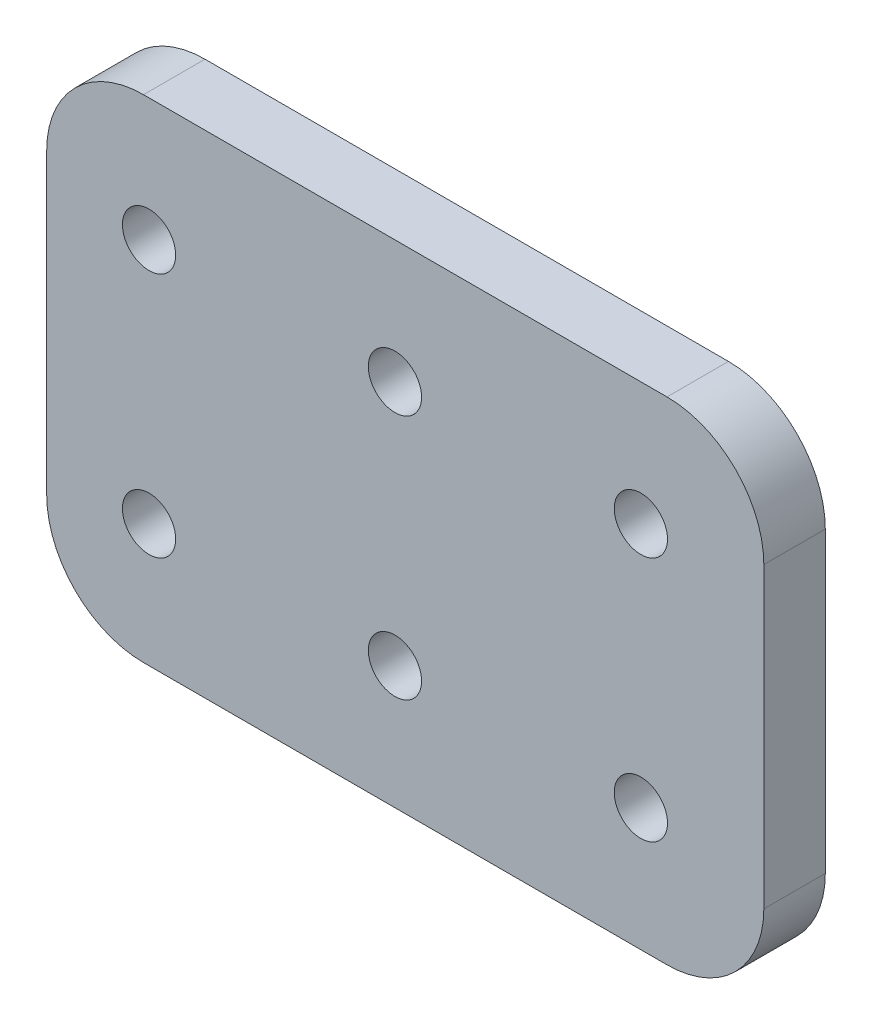
SolidWorks part; units mm, degrees
material "6061-T6 (SS)"
ref_plane "Front" through (0, 0, 0) normal (0, 0, 1) x (1, 0, 0)
ref_plane "Top" through (0, 0, 0) normal (0, 1, 0) x (1, 0, 0)
ref_plane "Right" through (0, 0, 0) normal (1, 0, 0) x (0, 0, -1)
sketch "Sketch1" plane through (0, 0, 0) normal (0, 0, 1) x (1, 0, 0)
  line L0 (-37.035, 25.4) -> (-39.165, 25.4) construction
  line L1 (37.035, -25.4) -> (-37.035, -25.4)
  line L2 (37.035, -25.4) -> (37.035, 25.4)
  line L3 (37.035, 25.4) -> (-37.035, 25.4)
  line L4 (-37.035, -25.4) -> (-37.035, 25.4)
  line L5 (37.035, -25.4) -> (-37.035, 25.4) construction
  line L6 (37.035, 25.4) -> (-37.035, -25.4) construction
  line L7 (-39.165, 25.4) -> (-39.165, -25.4) construction
  line L8 (-39.165, -25.4) -> (-37.035, -25.4) construction
  line L9 (-13.765, 25.4) -> (-13.765, -25.4) construction
  line L10 (-13.765, 0) -> (-39.165, 0) construction
  line L11 (-26.465, 0) -> (-26.465, 25.4) construction
  line L12 (24.335, 25.4) -> (24.335, -25.4) construction
  line L13 (-1.065, 25.4) -> (-1.065, -25.4) construction
  line L14 (-26.465, 12.7) -> (37.035, 12.7) construction
  line L15 (-26.465, -12.7) -> (37.035, -12.7) construction
  circle A0 centre (-26.465, 12.7) radius 2.5 construction
  circle A1 centre (-26.465, -12.7) radius 2.5 construction
  circle A2 centre (-1.065, 12.7) radius 2.5 construction
  circle A3 centre (24.335, 12.7) radius 2.5 construction
  circle A4 centre (24.335, -12.7) radius 2.5 construction
  circle A5 centre (-1.065, -12.7) radius 2.5 construction
  point P0 (0, 0)
  dimension "D5" = 5
  dimension "D8" = 5
  dimension "D1" = 2.13
  dimension "D2" = 25.4
  dimension "D3" = 50.8
  dimension "D4" = 76.2
  dimension "D6" = 12.7
  dimension "D7" = 25.4
extrude "Boss-Extrude1" add sketch "Sketch1" along normal blind 6.35
fillet "Fillet1" radius 10 4 edges at (-37.035, -25.4, 3.175) (37.035, -25.4, 3.175) (37.035, 25.4, 3.175) (-37.035, 25.4, 3.175)
hole_wizard "M5 Clearance Hole1" positions "Sketch3" profile "Sketch2" hole size "M5" standard "ISO" end condition through all
sketch "Sketch3" plane through (0, 0, 6.35) normal (0, 0, 1) x (1, 0, 0)
  point P0 (-26.465, 12.7)
  point P3 (-26.465, -12.7)
  point P6 (-1.065, -12.7)
  point P9 (-1.065, 12.7)
  point P12 (24.335, 12.7)
  point P15 (24.335, -12.7)
sketch "Sketch2" plane through (-26.465, 12.7, 6.35) normal (1, 0, 0) x (0, -1, 0)
  line L0 (0, 0) -> (0, 6.35)
  line L1 (0, 6.35) -> (2.75, 6.35)
  line L2 (2.75, 6.35) -> (2.75, 0)
  line L5 (2.75, 0) -> (0, 0)
  line L11 (0, -6.35) -> (0, 107.95) construction
  dimension "Thru Hole Dia." = 5.5
  dimension "Thru Hole Depth" = 6.35
